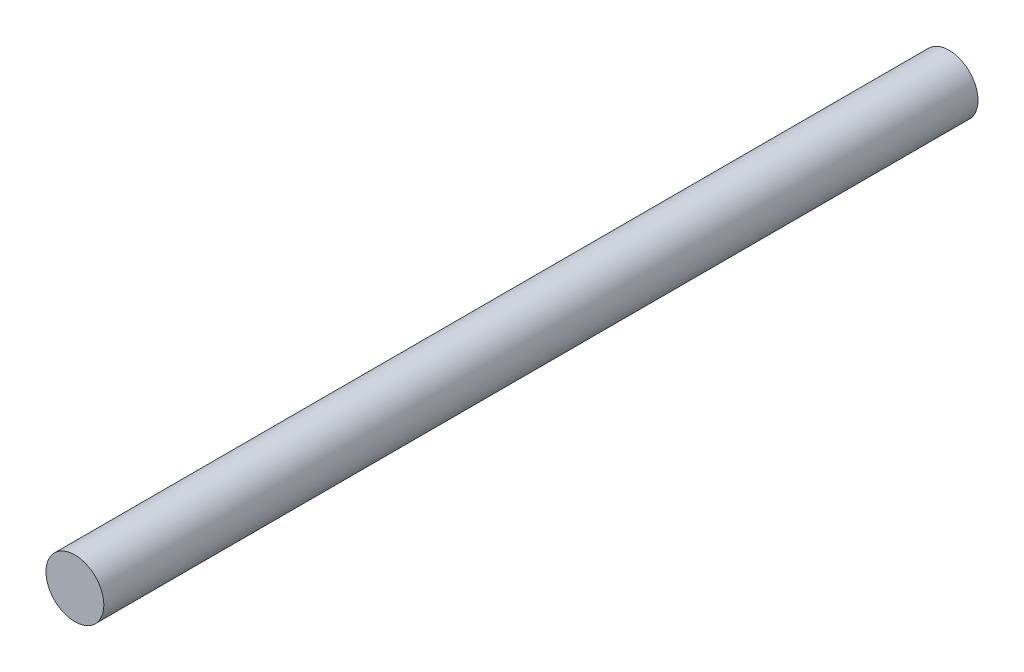
SolidWorks part; units mm, degrees
material "AISI 1020"
ref_plane "Спереди" through (0, 0, 0) normal (0, 0, 1) x (1, 0, 0)
ref_plane "Сверху" through (0, 0, 0) normal (0, 1, 0) x (1, 0, 0)
ref_plane "Справа" through (0, 0, 0) normal (1, 0, 0) x (0, 0, -1)
sketch "Эскиз1" plane through (0, 0, 0) normal (0, 0, 1) x (1, 0, 0)
  circle A0 centre (0, 0) radius 5
  dimension "D1" = 10
extrude "Бобышка-Вытянуть1" add sketch "Эскиз1" along normal blind 25 and the other way offset from surface (126 mm away) 50
cosmetic thread "Условное изображение резьбы1" parameters "D2"=8.344
cosmetic thread "Условное изображение резьбы2" parameters "D1"=5, "D2"=8.344
